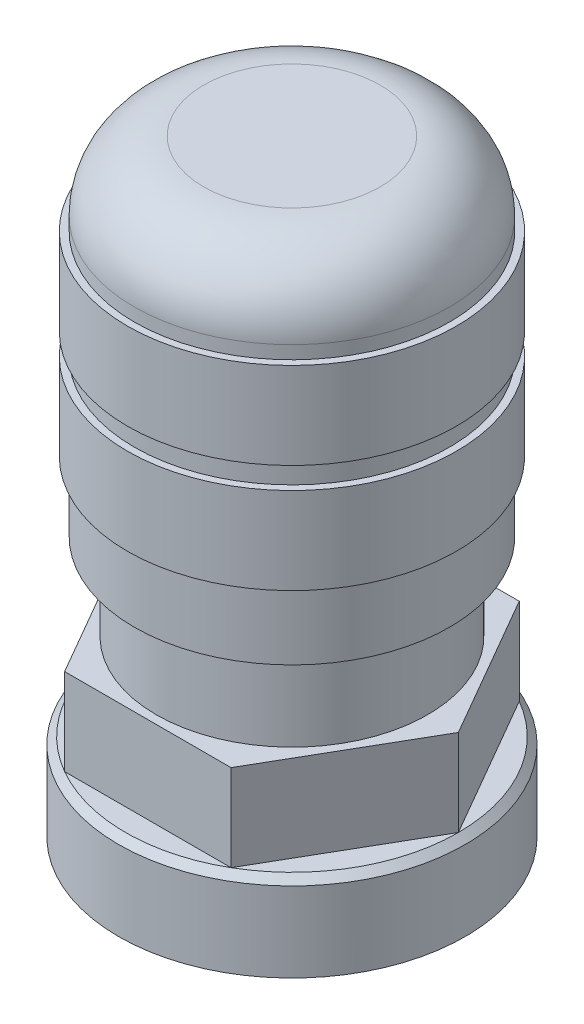
SolidWorks part; units mm, degrees
material "Chrome Stainless Steel"
ref_plane "Front" through (0, 0, 0) normal (0, 0, 1) x (1, 0, 0)
ref_plane "Top" through (0, 0, 0) normal (0, 1, 0) x (1, 0, 0)
ref_plane "Right" through (0, 0, 0) normal (1, 0, 0) x (0, 0, -1)
sketch "Sketch1" plane through (0, 0, 0) normal (0, 1, 0) x (1, 0, 0)
  circle A0 centre (0, 0) radius 6.35
  dimension "D1" = 12.7
extrude "Extrude1" add sketch "Sketch1" against normal blind 3.175
chamfer "Chamfer1" distance 0.254 angle 45 1 edges at (0, 0, 6.35)
sketch "Sketch2" plane through (0, 0, 0) normal (0, 1, 0) x (-1, 0, 0)
  line L1 (-6.096, 0) -> (-3.048, -5.2793)
  line L2 (-3.048, -5.2793) -> (3.048, -5.2793)
  line L3 (3.048, -5.2793) -> (6.096, 0)
  line L4 (6.096, 0) -> (3.048, 5.2793)
  line L5 (3.048, 5.2793) -> (-3.048, 5.2793)
  line L6 (-3.048, 5.2793) -> (-6.096, 0)
  circle A0 centre (0, 0) radius 5.2793 construction
extrude "Extrude2" add sketch "Sketch2" along normal blind 3.175
sketch "Sketch4" plane through (0, 0, 0) normal (1, 0, 0) x (0, 0, -1)
  line L0 (-4.9723, 3.175) -> (-4.9723, 6.35)
  line L1 (-5.2793, 3.175) -> (0, 3.175) construction
  line L2 (-4.9723, 6.35) -> (-5.7726, 6.35)
  line L3 (-5.7726, 6.35) -> (-5.7726, 8.8875)
  line L4 (-5.7726, 8.8875) -> (-6.0266, 8.8875)
  line L5 (-6.0266, 8.8875) -> (-6.0266, 12.0625)
  line L6 (-6.0266, 12.0625) -> (-5.7726, 12.0625)
  line L7 (-5.7726, 12.0625) -> (-5.7726, 12.8562)
  line L8 (-5.7726, 12.8562) -> (-6.0266, 12.8562)
  line L9 (-6.0266, 12.8562) -> (-6.0266, 16.0312)
  line L10 (-6.0266, 16.0312) -> (-5.7726, 16.0312)
  line L11 (-5.7726, 16.0312) -> (-5.7726, 16.51)
  line L12 (-3.2326, 19.05) -> (0, 19.05)
  line L13 (-3.7023, 4.445) -> (0, 4.445)
  line L14 (-4.9723, 3.175) -> (0, 3.175)
  line L15 (-3.7023, 4.445) -> (-3.7023, 7.62)
  line L16 (-3.7023, 7.62) -> (-4.5026, 7.62)
  line L17 (-4.5026, 7.62) -> (-4.5026, 10.1575)
  line L18 (-4.5026, 10.1575) -> (-4.7566, 10.1575)
  line L19 (-4.7566, 10.1575) -> (-4.7566, 10.7925)
  line L20 (-4.7566, 10.7925) -> (-4.5026, 10.7925)
  line L21 (-4.5026, 10.7925) -> (-4.5026, 14.1262)
  line L22 (-4.5026, 14.1262) -> (-4.7566, 14.1262)
  line L23 (-4.7566, 14.1262) -> (-4.7566, 14.7612)
  line L24 (-4.7566, 14.7612) -> (-4.5026, 14.7612)
  line L25 (-4.5026, 14.7612) -> (-4.5026, 16.51)
  line L26 (-3.2326, 17.78) -> (0, 17.78)
  line L27 (0, 19.05) -> (0, 17.78)
  line L28 (0, 4.445) -> (0, 3.175)
  line L29 (0, 20.1696) -> (0, 0.7082) construction
  arc A0 (-5.7726, 16.51) -> (-3.2326, 19.05) centre (-3.2326, 16.51) cw
  arc A1 (-4.5026, 16.51) -> (-3.2326, 17.78) centre (-3.2326, 16.51) cw
  dimension "D6" = 2.54
  dimension "D1" = 12.7
  dimension "D2" = 3.175
  dimension "D3" = 0.7937
  dimension "D4" = 3.175
  dimension "D5" = 0.254
  dimension "D7" = 1.27
revolve "Revolve1" add sketch "Sketch4" angle 360 about L29
sketch "Sketch5" plane through (0, -3.175, 0) normal (0, -1, 0) x (1, 0, 0)
  circle A0 centre (0, 0) radius 3.9688
  dimension "D1" = 7.9375
extrude "Extrude4" cut sketch "Sketch5" against normal blind 12.7
